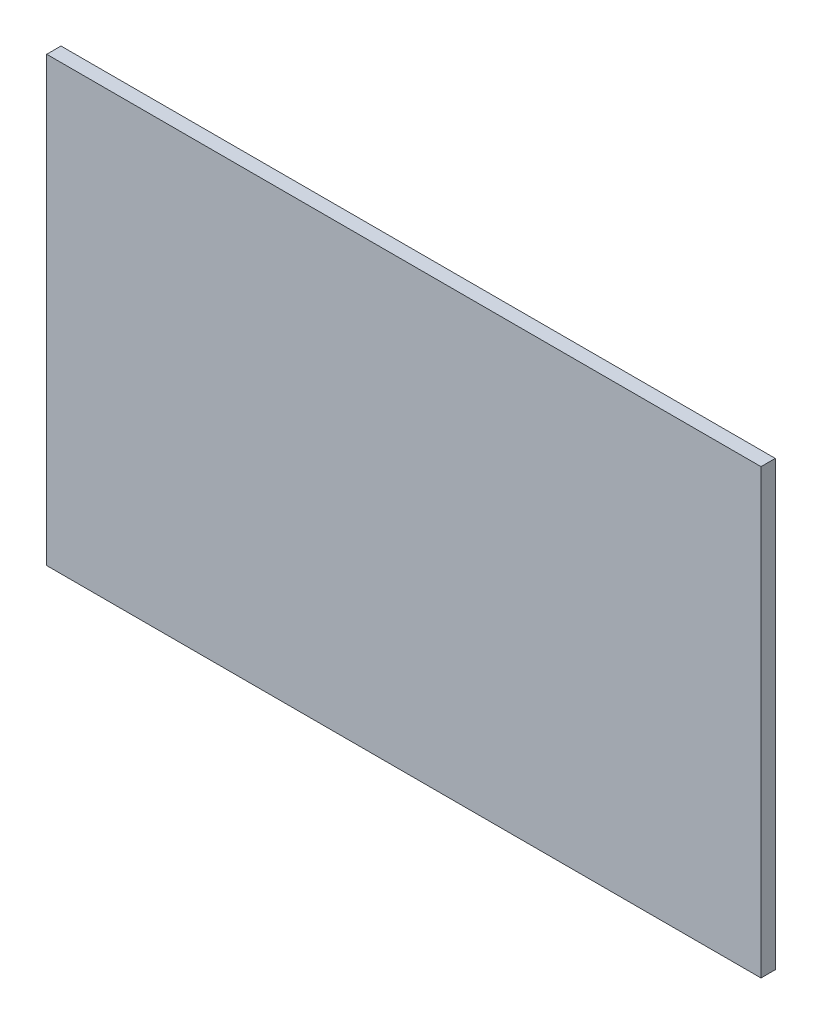
SolidWorks part; units mm, degrees
ref_plane "Ön Düzlem" through (0, 0, 0) normal (0, 0, 1) x (1, 0, 0)
ref_plane "Üst Düzlem" through (0, 0, 0) normal (0, 1, 0) x (1, 0, 0)
ref_plane "Sağ Düzlem" through (0, 0, 0) normal (1, 0, 0) x (0, 0, -1)
sketch "Sketch1" plane through (0, 0, 0) normal (0, 0, 1) x (1, 0, 0)
  line L1 (-250, 155) -> (250, 155)
  line L2 (-250, 155) -> (-250, -155)
  line L3 (-250, -155) -> (250, -155)
  line L4 (250, 155) -> (250, -155)
  line L5 (-250, 155) -> (250, -155) construction
  line L6 (-250, -155) -> (250, 155) construction
  point P0 (0, 0)
  dimension "D1" = 500
  dimension "D2" = 310
extrude "Boss-Extrude1" add sketch "Sketch1" along normal blind 10
